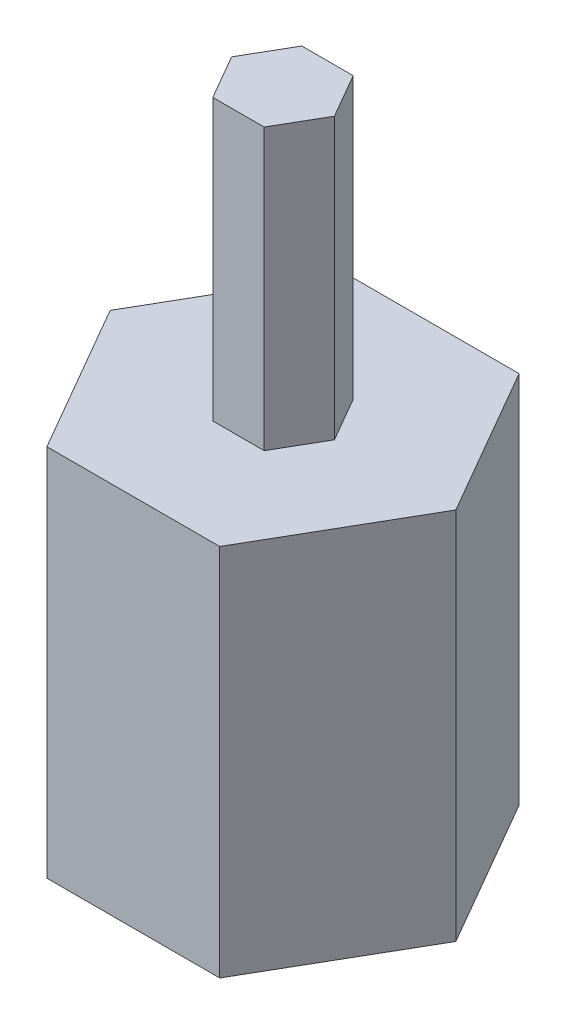
SolidWorks part; units mm, degrees
ref_plane "Front Plane" through (0, 0, 0) normal (0, 0, 1) x (1, 0, 0)
ref_plane "Top Plane" through (0, 0, 0) normal (0, 1, 0) x (1, 0, 0)
ref_plane "Right Plane" through (0, 0, 0) normal (1, 0, 0) x (0, 0, -1)
sketch "Sketch1" plane through (0, 0, 0) normal (0, 1, 0) x (1, 0, 0)
  line L1 (1.1, 0) -> (0.55, 0.9526)
  line L2 (0.55, 0.9526) -> (-0.55, 0.9526)
  line L3 (-0.55, 0.9526) -> (-1.1, 0)
  line L4 (-1.1, 0) -> (-0.55, -0.9526)
  line L5 (-0.55, -0.9526) -> (0.55, -0.9526)
  line L6 (0.55, -0.9526) -> (1.1, 0)
  circle A0 centre (0, 0) radius 0.9526 construction
  dimension "D1" = 1.1
extrude "Boss-Extrude1" add sketch "Sketch1" along normal blind 6
sketch "Sketch2" plane through (0, 0, 0) normal (0, -1, 0) x (1, 0, 0)
  line L1 (3.7, 0) -> (1.85, 3.2043)
  line L2 (1.85, 3.2043) -> (-1.85, 3.2043)
  line L3 (-1.85, 3.2043) -> (-3.7, 0)
  line L4 (-3.7, 0) -> (-1.85, -3.2043)
  line L5 (-1.85, -3.2043) -> (1.85, -3.2043)
  line L6 (1.85, -3.2043) -> (3.7, 0)
  circle A0 centre (0, 0) radius 3.2043 construction
  circle A1 centre (0, 0) radius 3.7 construction
  dimension "D1" = 7.4
extrude "Boss-Extrude2" add sketch "Sketch2" along normal blind 8
